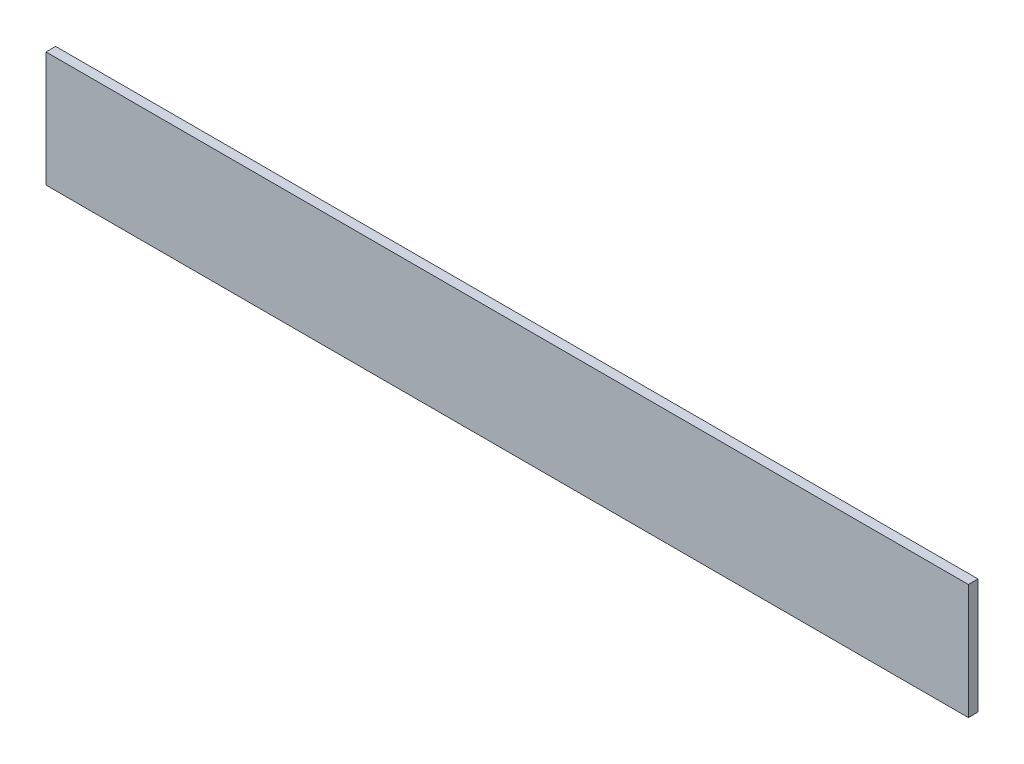
SolidWorks part; units mm, degrees
material "PVC 0.007 Plasticized"
ref_plane "Front Plane" through (0, 0, 0) normal (0, 0, 1) x (1, 0, 0)
ref_plane "Top Plane" through (0, 0, 0) normal (0, 1, 0) x (1, 0, 0)
ref_plane "Right Plane" through (0, 0, 0) normal (1, 0, 0) x (0, 0, -1)
sketch "Sketch1" plane through (0, 0, 0) normal (1, 0, 0) x (0, 0, -1)
  line L1 (-3.175, -38.1) -> (3.175, -38.1)
  line L2 (-3.175, -38.1) -> (-3.175, 38.1)
  line L3 (-3.175, 38.1) -> (3.175, 38.1)
  line L4 (3.175, -38.1) -> (3.175, 38.1)
  line L5 (-3.175, -38.1) -> (3.175, 38.1) construction
  line L6 (-3.175, 38.1) -> (3.175, -38.1) construction
  point P0 (0, 0)
  dimension "D1" = 76.2
  dimension "D2" = 6.35
extrude "Boss-Extrude1" add sketch "Sketch1" along normal blind 609.6
equation "\"D2@Sketch1\"=1in/4"
